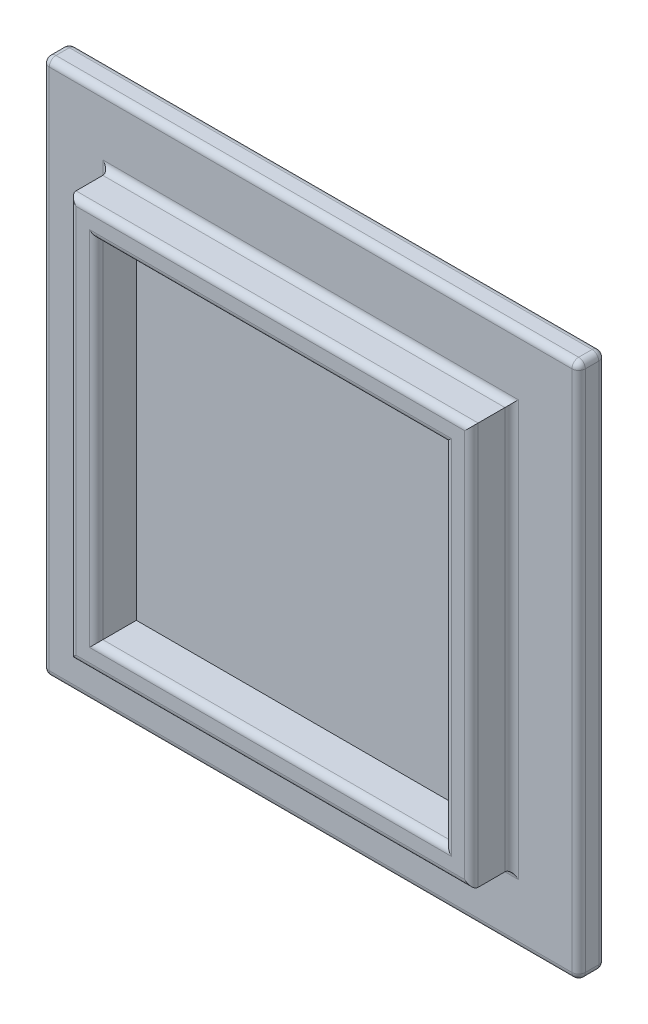
SolidWorks part; units mm, degrees
ref_plane "Front Plane" through (0, 0, 0) normal (0, 0, 1) x (1, 0, 0)
ref_plane "Top Plane" through (0, 0, 0) normal (0, 1, 0) x (1, 0, 0)
ref_plane "Right Plane" through (0, 0, 0) normal (1, 0, 0) x (0, 0, -1)
sketch "Sketch1" plane through (0, 0, 0) normal (0, 0, 1) x (1, 0, 0)
  line L1 (-25.1923, 20.7012) -> (14.8077, 20.7012)
  line L2 (-25.1923, 20.7012) -> (-25.1923, -19.2988)
  line L3 (-25.1923, -19.2988) -> (14.8077, -19.2988)
  line L4 (14.8077, 20.7012) -> (14.8077, -19.2988)
  dimension "D1" = 40
  dimension "D2" = 40
extrude "Boss-Extrude1" add sketch "Sketch1" along normal blind 2
sketch "Sketch2" plane through (0, 0, 2) normal (0, 0, 1) x (1, 0, 0)
  line L0 (-22.4138, 17.9227) -> (14.8077, -19.2988) construction
  line L1 (-25.1923, -19.2988) -> (14.8077, 20.7012) construction
  line L3 (9.8077, -14.2988) -> (-20.1923, -14.2988)
  line L4 (9.8077, -14.2988) -> (9.8077, 15.7012)
  line L5 (9.8077, 15.7012) -> (-20.1923, 15.7012)
  line L6 (-20.1923, -14.2988) -> (-20.1923, 15.7012)
  line L7 (9.8077, -14.2988) -> (-20.1923, 15.7012) construction
  line L8 (9.8077, 15.7012) -> (-20.1923, -14.2988) construction
  line L9 (7.8077, -12.2988) -> (-18.1923, -12.2988)
  line L10 (7.8077, -12.2988) -> (7.8077, 13.7012)
  line L11 (7.8077, 13.7012) -> (-18.1923, 13.7012)
  line L12 (-18.1923, -12.2988) -> (-18.1923, 13.7012)
  line L13 (7.8077, -12.2988) -> (-18.1923, 13.7012) construction
  line L14 (7.8077, 13.7012) -> (-18.1923, -12.2988) construction
  point P8 (-5.1923, 0.7012)
  point P9 (-5.1923, 0.7012)
  point P14 (-5.1923, 0.7012)
  dimension "D1" = 30
  dimension "D2" = 26
extrude "Boss-Extrude2" add sketch "Sketch2" along normal blind 3
fillet "Fillet1" radius 0.5 8 edges at (7.8077, 0.7012, 5) (-5.1923, 13.7012, 5) (-18.1923, 0.7012, 5) (-5.1923, -12.2988, 5) (-5.1923, -14.2988, 5) (-20.1923, 0.7012, 5) (9.8077, 0.7012, 5) (-5.1923, 15.7012, 5)
fillet "Fillet2" radius 0.5 12 edges at (14.8077, 20.7012, 1) (-5.1923, 20.7012, 2) (-5.1923, 20.7012, 0) (-25.1923, 20.7012, 1) (-25.1923, -19.2988, 1) (-25.1923, 0.7012, 0) (-25.1923, 0.7012, 2) (-5.1923, -19.2988, 0) (-5.1923, -19.2988, 2) (14.8077, 0.7012, 2) (14.8077, 0.7012, 0) (14.8077, -19.2988, 1)
fillet "Fillet3" radius 0.5 4 edges at (-5.1923, -14.2988, 2) (9.8077, 0.7012, 2) (-5.1923, 15.7012, 2) (-20.1923, 0.7012, 2)
